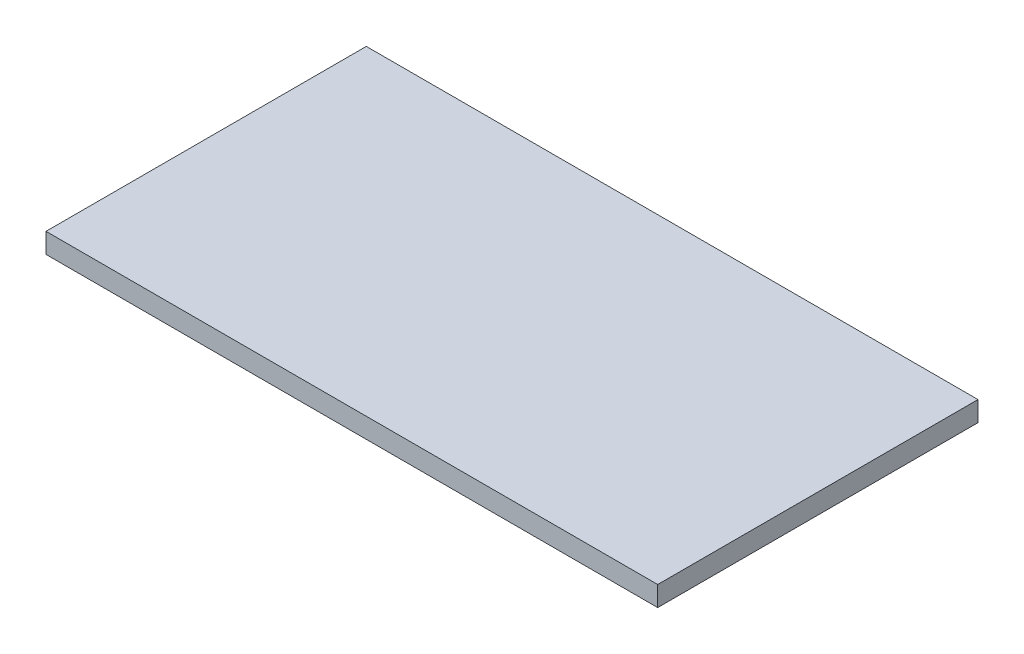
SolidWorks part; units mm, degrees
ref_plane "Front Plane" through (0, 0, 0) normal (0, 0, 1) x (1, 0, 0)
ref_plane "Top Plane" through (0, 0, 0) normal (0, 1, 0) x (1, 0, 0)
ref_plane "Right Plane" through (0, 0, 0) normal (1, 0, 0) x (0, 0, -1)
sketch "Sketch1" plane through (0, 0, 0) normal (0, 1, 0) x (1, 0, 0)
  line L1 (275, -144) -> (-275, -144)
  line L2 (275, -144) -> (275, 144)
  line L3 (275, 144) -> (-275, 144)
  line L4 (-275, -144) -> (-275, 144)
  line L5 (275, -144) -> (-275, 144) construction
  line L6 (275, 144) -> (-275, -144) construction
  point P0 (0, 0)
  dimension "D1" = 288
  dimension "D2" = 550
extrude "Boss-Extrude1" add sketch "Sketch1" along normal blind 18
equation "\"H_DSP\"=18"
equation "\"D1@Boss-Extrude1\"=\"H_DSP\""
